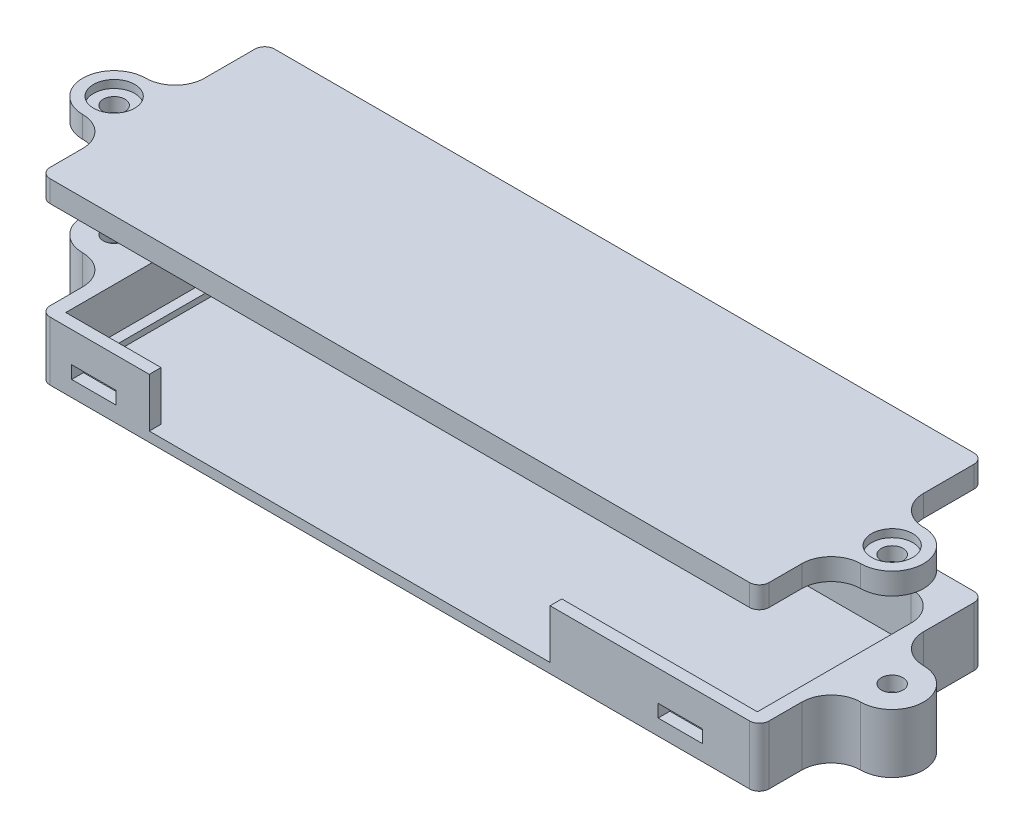
SolidWorks part; units mm, degrees
ref_plane "前视基准面" through (0, 0, 0) normal (0, 0, 1) x (1, 0, 0)
ref_plane "上视基准面" through (0, 0, 0) normal (0, 1, 0) x (1, 0, 0)
ref_plane "右视基准面" through (0, 0, 0) normal (1, 0, 0) x (0, 0, -1)
sketch "草图1" plane through (0, 0, 0) normal (0, 1, 0) x (1, 0, 0)
  line L1 (-35.2, -9.325) -> (35.2, -9.325)
  line L2 (-35.2, -9.325) -> (-35.2, 9.325)
  line L3 (-35.2, 9.325) -> (32.2, 9.325)
  line L4 (35.2, -9.325) -> (35.2, 6.325)
  line L5 (-35.2, -9.325) -> (35.2, 9.325) construction
  line L6 (-35.2, 9.325) -> (35.2, -9.325) construction
  line L7 (-36.6, 12.325) -> (36.6, 12.325)
  line L8 (-36.6, 12.325) -> (-36.6, -10.525)
  line L9 (-36.6, -10.525) -> (36.6, -10.525)
  line L10 (36.6, 12.325) -> (36.6, -10.525)
  arc A0 (35.2, 6.325) -> (32.2, 9.325) centre (32.2, 6.325) ccw
  point P0 (0, 0)
  point P10 (0, -10.525)
  dimension "D6" = 3
  dimension "D1" = 70.4
  dimension "D2" = 18.65
  dimension "D3" = 1.4
  dimension "D4" = 1.2
  dimension "D5" = 3
extrude "凸台-拉伸1" add sketch "草图1" along normal blind 5
sketch "草图2" plane through (0, 0, 0) normal (0, -1, 0) x (1, 0, 0)
  line L1 (-36.6, 10.525) -> (36.6, 10.525)
  line L2 (-36.6, 10.525) -> (-36.6, -12.325)
  line L3 (-36.6, -12.325) -> (36.6, -12.325)
  line L4 (36.6, 10.525) -> (36.6, -12.325)
extrude "凸台-拉伸2" add sketch "草图2" along normal blind 1
sketch "草图3" plane through (0, 0, 0) normal (0, 1, 0) x (1, 0, 0)
  line L0 (-35.2, 9.325) -> (-35.2, -9.325) construction
  line L1 (-35.2, 7.2792) -> (-34.2, 7.2792)
  line L2 (-35.2, 7.2792) -> (-35.2, -7.2911)
  line L3 (-35.2, -7.2911) -> (-34.2, -7.2911)
  line L4 (-34.2, 7.2792) -> (-34.2, -7.2911)
  line L5 (0, 0) -> (0, -2.837) construction
  line L6 (-35.2, 9.325) -> (-35.2, -9.325) construction
  line L7 (35.2, -7.2911) -> (34.2, -7.2911)
  line L8 (34.2, 7.2792) -> (34.2, -7.2911)
  line L9 (35.2, 7.2792) -> (34.2, 7.2792)
  line L10 (35.2, 7.2792) -> (35.2, -7.2911)
  dimension "D1" = 1
extrude "凸台-拉伸3" add sketch "草图3" along normal blind 0.6
sketch "草图4" plane through (0, 0, -12.325) normal (0, 0, -1) x (-1, 0, 0)
  line L1 (17.95, 5) -> (28.9, 5)
  line L2 (17.95, 5) -> (17.95, 0)
  line L3 (17.95, 0) -> (28.9, 0)
  line L4 (28.9, 5) -> (28.9, 0)
  line L5 (35.2, 5) -> (35.2, 0) construction
  line L6 (-32.2, 0) -> (35.2, 0) construction
  line L7 (-36.6, 5) -> (36.6, 5) construction
  point P6 (17.95, 2.5)
  dimension "D1" = 6.3
  dimension "D2" = 17.25
extrude "切除-拉伸1" cut sketch "草图4" against normal up to next
sketch "草图5" plane through (0, 0, 10.525) normal (0, 0, 1) x (1, 0, 0)
  line L0 (-35.2, 0) -> (35.2, 0) construction
  line L1 (-25.5, 0) -> (15.3, 0)
  line L2 (-25.5, 0) -> (-25.5, 5)
  line L3 (-25.5, 5) -> (15.3, 5)
  line L4 (15.3, 0) -> (15.3, 5)
  line L5 (-36.6, 5) -> (36.6, 5) construction
  line L6 (-35.2, 5) -> (-35.2, 0) construction
  line L7 (-35.2, 0.6) -> (-34.2, 0.6) construction
  line L8 (-28.9, 0.6) -> (-33.4, 0.6)
  line L9 (-28.9, 0.6) -> (-28.9, 1.9)
  line L10 (-28.9, 1.9) -> (-33.4, 1.9)
  line L11 (-33.4, 0.6) -> (-33.4, 1.9)
  line L12 (26.3, 0.6) -> (30.8, 0.6)
  line L13 (26.3, 0.6) -> (26.3, 1.9)
  line L14 (26.3, 1.9) -> (30.8, 1.9)
  line L15 (30.8, 0.6) -> (30.8, 1.9)
  dimension "D1" = 9.7
  dimension "D2" = 50.5
  dimension "D3" = 1.3
  dimension "D4" = 4.5
  dimension "D5" = 1.8
  dimension "D6" = 61.5
extrude "切除-拉伸2" cut sketch "草图5" against normal up to next
fillet "圆角1" radius 1 4 edges at (-36.6, 2, 10.525) (36.6, 2, 10.525) (36.6, 2, -12.325) (-36.6, 2, -12.325)
sketch "草图6" plane through (0, 5, 0) normal (0, 1, 0) x (1, 0, 0)
  line L0 (0, 0) -> (0, 17.6229) construction
  line L1 (-36.6, 11.325) -> (-36.6, -9.525) construction
  line L2 (-35.2, 9.325) -> (-35.2, -9.325) construction
  line L3 (-36.6, 6.2) -> (-36.6, -6.2)
  line L4 (36.6, 6.2) -> (36.6, -6.2)
  circle A0 centre (-39.6, 0) radius 1.1
  arc A2 (-39.6, 3.2) -> (-39.6, -3.2) centre (-39.6, 0) ccw
  arc A3 (-39.6, 3.2) -> (-36.6, 6.2) centre (-39.6, 6.2) ccw
  arc A4 (-39.6, -3.2) -> (-36.6, -6.2) centre (-39.6, -6.2) cw
  circle A5 centre (39.6, 0) radius 1.1
  arc A6 (39.6, 3.2) -> (36.6, 6.2) centre (39.6, 6.2) cw
  arc A7 (39.6, 3.2) -> (39.6, -3.2) centre (39.6, 0) cw
  arc A8 (39.6, -3.2) -> (36.6, -6.2) centre (39.6, -6.2) ccw
  point P13 (-35.2, 0)
  dimension "D2" = 2.2
  dimension "D3" = 3.2
  dimension "D1" = 3
extrude "凸台-拉伸4" add sketch "草图6" against normal up to surface (6 mm away) up to face at (0, -1, -0.9)
sketch "草图7" plane through (0, -1, 0) normal (0, -1, 0) x (1, 0, 0)
  line L1 (-37.55, 1.1836) -> (-39.6, 2.3671)
  line L2 (-39.6, 2.3671) -> (-41.65, 1.1836)
  line L3 (-41.65, 1.1836) -> (-41.65, -1.1836)
  line L4 (-41.65, -1.1836) -> (-39.6, -2.3671)
  line L5 (-39.6, -2.3671) -> (-37.55, -1.1836)
  line L6 (-37.55, -1.1836) -> (-37.55, 1.1836)
  line L7 (39.6, 2.3671) -> (37.55, 1.1836)
  line L8 (37.55, 1.1836) -> (37.55, -1.1836)
  line L9 (37.55, -1.1836) -> (39.6, -2.3671)
  line L10 (39.6, -2.3671) -> (41.65, -1.1836)
  line L11 (41.65, -1.1836) -> (41.65, 1.1836)
  line L12 (41.65, 1.1836) -> (39.6, 2.3671)
  circle A0 centre (-39.6, 0) radius 2.05 construction
  circle A1 centre (39.6, 0) radius 2.05 construction
  dimension "D1" = 4.1
extrude "切除-拉伸3" cut sketch "草图7" against normal offset from surface (4.5 mm away) 1.5 up to face at (-34.1694, 5, -0.3857)
ref_plane "基准面1" through (0, 15, 0) normal (0, 1, 0) x (1, 0, 0)
sketch "草图8" plane through (0, 15, 0) normal (0, 1, 0) x (1, 0, 0)
  line L0 (36.6, -9.525) -> (36.6, -6.2) construction
  line L1 (36.6, 6.2) -> (36.6, 11.325) construction
  line L2 (-36.6, -6.2) -> (-36.6, -9.525) construction
  line L3 (-36.6, 11.325) -> (-36.6, 6.2) construction
  line L4 (36.6, -9.525) -> (36.6, -6.2)
  line L5 (36.6, 6.2) -> (36.6, 11.325)
  line L6 (-36.6, -6.2) -> (-36.6, -9.525)
  line L7 (-36.6, 11.325) -> (-36.6, 6.2)
  line L8 (-35.6, 12.325) -> (35.6, 12.325)
  line L9 (-35.6, -10.525) -> (35.6, -10.525)
  arc A0 (39.6, -3.2) -> (36.6, -6.2) centre (39.6, -6.2) ccw construction
  arc A1 (39.6, -3.2) -> (39.6, 3.2) centre (39.6, 0) ccw construction
  arc A2 (36.6, 6.2) -> (39.6, 3.2) centre (39.6, 6.2) ccw construction
  arc A3 (36.6, 11.325) -> (35.6, 12.325) centre (35.6, 11.325) ccw construction
  arc A4 (-35.6, 12.325) -> (-36.6, 11.325) centre (-35.6, 11.325) ccw construction
  arc A5 (-36.6, -9.525) -> (-35.6, -10.525) centre (-35.6, -9.525) ccw construction
  arc A6 (-36.6, -6.2) -> (-39.6, -3.2) centre (-39.6, -6.2) ccw construction
  arc A7 (-39.6, 3.2) -> (-39.6, -3.2) centre (-39.6, 0) ccw construction
  arc A8 (-39.6, 3.2) -> (-36.6, 6.2) centre (-39.6, 6.2) ccw construction
  arc A9 (39.6, -3.2) -> (36.6, -6.2) centre (39.6, -6.2) ccw
  arc A10 (39.6, -3.2) -> (39.6, 3.2) centre (39.6, 0) ccw
  arc A11 (36.6, 6.2) -> (39.6, 3.2) centre (39.6, 6.2) ccw
  arc A12 (36.6, 11.325) -> (35.6, 12.325) centre (35.6, 11.325) ccw
  arc A13 (-35.6, 12.325) -> (-36.6, 11.325) centre (-35.6, 11.325) ccw
  arc A14 (-36.6, -9.525) -> (-35.6, -10.525) centre (-35.6, -9.525) ccw
  arc A15 (-36.6, -6.2) -> (-39.6, -3.2) centre (-39.6, -6.2) ccw
  arc A16 (-39.6, 3.2) -> (-39.6, -3.2) centre (-39.6, 0) ccw
  arc A17 (-39.6, 3.2) -> (-36.6, 6.2) centre (-39.6, 6.2) ccw
  arc A18 (35.6, -10.525) -> (36.6, -9.525) centre (35.6, -9.525) ccw construction
  arc A19 (35.6, -10.525) -> (36.6, -9.525) centre (35.6, -9.525) ccw
  circle A20 centre (39.6, 0) radius 1.1 construction
  circle A21 centre (-39.6, 0) radius 1.1 construction
  circle A22 centre (39.6, 0) radius 1.1
  circle A23 centre (-39.6, 0) radius 1.1
extrude "凸台-拉伸5" add sketch "草图8" along normal blind 2.2 separate body
sketch "草图9" plane through (0, 17.2, 0) normal (0, 1, 0) x (1, 0, 0)
  circle A0 centre (-39.6, 0) radius 2.1
  circle A1 centre (39.6, 0) radius 2.1
  dimension "D1" = 4.2
extrude "切除-拉伸4" cut sketch "草图9" against normal blind 0.8
